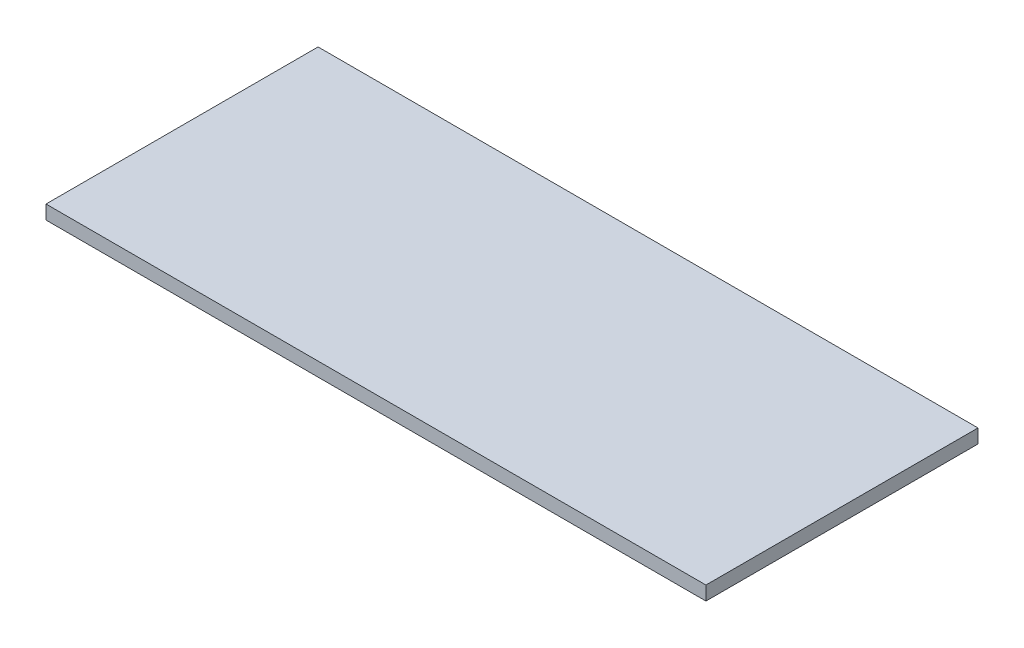
SolidWorks part; units mm, degrees
ref_plane "Front Plane" through (0, 0, 0) normal (0, 0, 1) x (1, 0, 0)
ref_plane "Top Plane" through (0, 0, 0) normal (0, 1, 0) x (1, 0, 0)
ref_plane "Right Plane" through (0, 0, 0) normal (1, 0, 0) x (0, 0, -1)
sketch "Sketch2" plane through (0, 0, 0) normal (0, 1, 0) x (1, 0, 0)
  line L1 (-836.6028, -165.8572) -> (-158.9062, -165.8572)
  line L2 (-836.6028, -165.8572) -> (-836.6028, -445.2572)
  line L3 (-836.6028, -445.2572) -> (-158.9062, -445.2572)
  line L4 (-158.9062, -165.8572) -> (-158.9062, -445.2572)
  dimension "D1" = 677.6966
  dimension "D2" = 279.4
extrude "Boss-Extrude2" add sketch "Sketch2" along normal blind 14.2875
